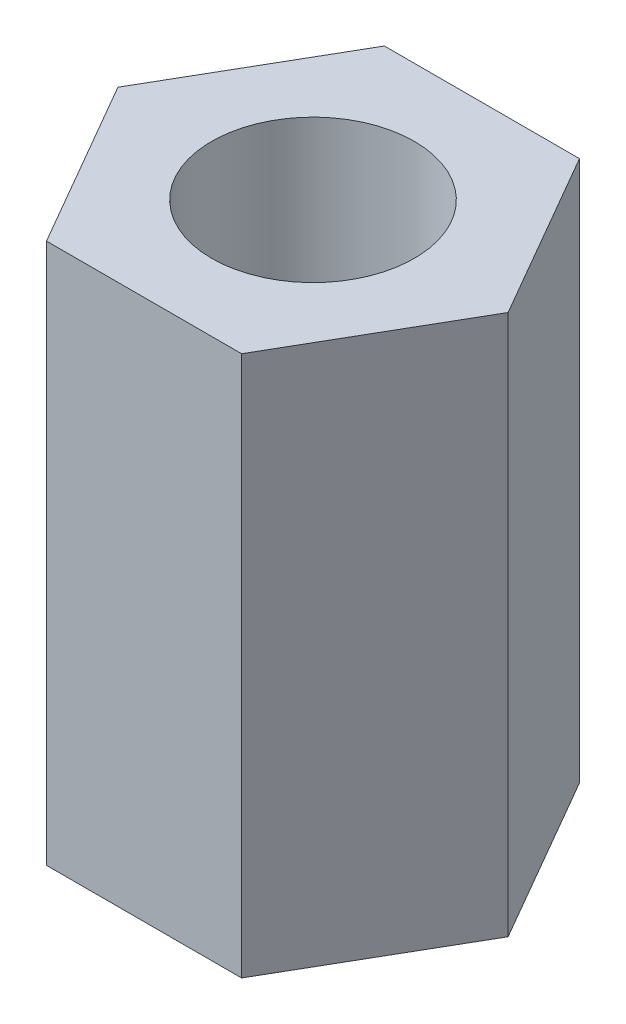
SolidWorks part; units mm, degrees
ref_plane "Front Plane" through (0, 0, 0) normal (0, 0, 1) x (1, 0, 0)
ref_plane "Top Plane" through (0, 0, 0) normal (0, 1, 0) x (1, 0, 0)
ref_plane "Right Plane" through (0, 0, 0) normal (1, 0, 0) x (0, 0, -1)
sketch "Sketch1" plane through (0, 0, 0) normal (0, 1, 0) x (1, 0, 0)
  line L1 (2.8868, 0) -> (1.4434, 2.5)
  line L2 (1.4434, 2.5) -> (-1.4434, 2.5)
  line L3 (-1.4434, 2.5) -> (-2.8868, 0)
  line L4 (-2.8868, 0) -> (-1.4434, -2.5)
  line L5 (-1.4434, -2.5) -> (1.4434, -2.5)
  line L6 (1.4434, -2.5) -> (2.8868, 0)
  circle A0 centre (0, 0) radius 2.5 construction
  circle A1 centre (0, 0) radius 1.5
  dimension "D2" = 3
  dimension "D1" = 5
extrude "Boss-Extrude1" add sketch "Sketch1" along normal blind 8 contours L5 L6 L1 L2 L3 L4 A1
